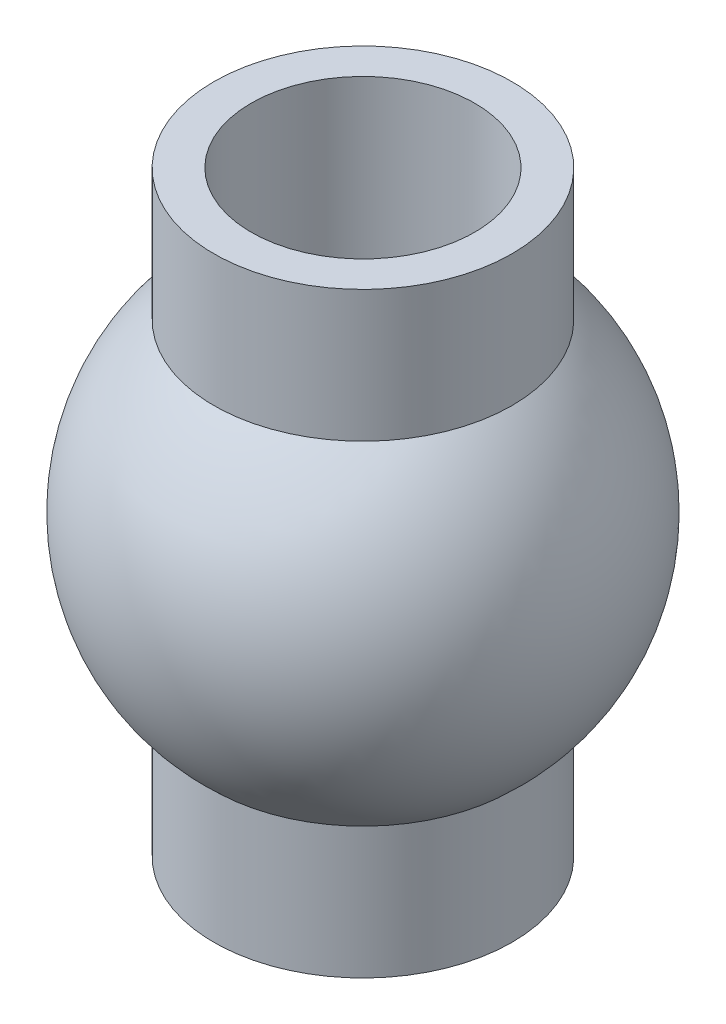
SolidWorks part; units mm, degrees
material "Chrome Stainless Steel"
ref_plane "Front Plane" through (0, 0, 0) normal (0, 0, 1) x (1, 0, 0)
ref_plane "Top Plane" through (0, 0, 0) normal (0, 1, 0) x (1, 0, 0)
ref_plane "Right Plane" through (0, 0, 0) normal (1, 0, 0) x (0, 0, -1)
sketch "Sketch1" plane through (0, 0, 0) normal (0, 0, 1) x (1, 0, 0)
  line L0 (1.5, -4) -> (1.5, 4)
  line L1 (1.5, 4) -> (2, 4)
  line L2 (2, 4) -> (2, 2.2361)
  line L3 (2, -2.2361) -> (2, -4)
  line L4 (2, -4) -> (1.5, -4)
  line L5 (0, 10.9319) -> (0, -7.2652) construction
  arc A0 (2, 2.2361) -> (2, -2.2361) centre (0, 0) cw
  point P7 (1.5, 0)
  dimension "D3" = 3
  dimension "D1" = 3
  dimension "D2" = 8
  dimension "D4" = 4
revolve "Revolve1" add sketch "Sketch1" angle 360 about L5
